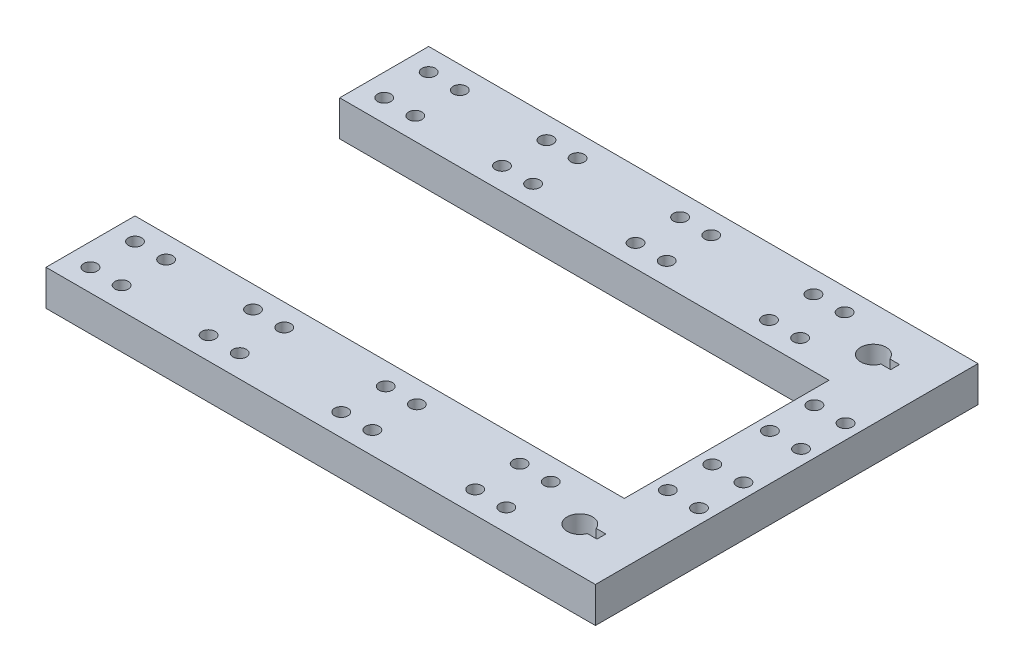
SolidWorks part; units mm, degrees
ref_plane "Front Plane" through (0, 0, 0) normal (0, 0, 1) x (1, 0, 0)
ref_plane "Top Plane" through (0, 0, 0) normal (0, 1, 0) x (1, 0, 0)
ref_plane "Right Plane" through (0, 0, 0) normal (1, 0, 0) x (0, 0, -1)
sketch "Sketch1" plane through (0, 0, 0) normal (0, 1, 0) x (1, 0, 0)
  line L0 (130.9822, 32.9968) -> (21, 32.9968)
  line L6 (130.9822, 32.9968) -> (130.9822, 40.4968)
  line L7 (21, 32.9968) -> (21, 42.9968)
  line L8 (21, 42.9968) -> (144.4822, 42.9968)
  line L9 (130.9822, 32.9968) -> (130.9822, -33.0032)
  line L10 (144.4822, 42.9968) -> (144.4822, 40.4968)
  line L11 (130.9822, -33.0032) -> (20.9822, -33.0032)
  line L12 (21, 32.9968) -> (21, 22.9968)
  line L13 (21, 22.9968) -> (144.4822, 22.9968)
  line L14 (20.9822, -33.0032) -> (20.9822, -23.0032)
  line L15 (20.9822, -23.0032) -> (144.4822, -23.0032)
  line L16 (130.9822, 32.9968) -> (144.4822, 32.9968)
  line L17 (144.4822, 32.9968) -> (144.4822, 40.4968)
  line L18 (144.4822, 40.4968) -> (130.9822, 40.4968)
  line L19 (144.4822, 32.9968) -> (144.4822, -40.5032)
  line L20 (144.4822, -40.5032) -> (130.9822, -40.5032)
  line L21 (20.9822, -33.0032) -> (20.9822, -43.0032)
  line L22 (20.9822, -43.0032) -> (144.4822, -43.0032)
  line L23 (144.4822, -43.0032) -> (144.4822, -40.5032)
  line L24 (26, 32.9968) -> (56, 32.9968)
  line L25 (133.85, 33.9968) -> (133.67, 33.9968)
  line L26 (26, 32.9968) -> (56, 32.9968)
  line L27 (133.85, 31.9968) -> (133.67, 31.9968)
  line L28 (130.9822, -33.0032) -> (133.8322, -33.0032)
  line L29 (56, 32.9968) -> (86, 32.9968)
  line L30 (86, 32.9968) -> (116, 32.9968)
  line L31 (133.8322, -32) -> (132.7951, -32)
  line L32 (133.8322, -34) -> (132.5224, -34)
  line L33 (21, 32.9968) -> (26, 32.9968)
  line L34 (26, 32.9968) -> (26, 27.9968)
  line L35 (26, 27.9968) -> (26, 37.9968)
  line L36 (26, 27.9968) -> (33, 27.9968)
  line L37 (20.9822, -33.0032) -> (25.9822, -33.0032)
  line L38 (25.9822, -33.0032) -> (25.9822, -28.0032)
  line L39 (25.9822, -28.0032) -> (25.9822, -38.0032)
  line L40 (25.9822, -38.0032) -> (32.9822, -38.0032)
  line L41 (133.85, 33.9968) -> (135.85, 33.9968)
  line L42 (135.85, 33.9968) -> (135.85, 31.9968)
  line L43 (135.85, 31.9968) -> (133.85, 31.9968)
  line L44 (133.8322, -32) -> (135.8322, -32)
  line L45 (135.8322, -32) -> (135.8322, -34)
  line L46 (135.8322, -34) -> (133.8322, -34)
  line L47 (25.9822, -33.0032) -> (55.9822, -33.0032)
  line L48 (55.9822, -33.0032) -> (85.9822, -33.0032)
  line L49 (85.9822, -33.0032) -> (115.9822, -33.0032)
  line L50 (144.4822, 22.9968) -> (137.7322, 22.9968)
  line L51 (137.7322, 22.9968) -> (137.7322, 11.4968)
  line L52 (137.7322, -23.0032) -> (137.7322, -11.5032)
  line L53 (132.5224, -34) -> (132.5224, -32)
  line L54 (132.5224, -32) -> (132.7951, -32)
  circle A6 centre (130.9822, 32.9968) radius 2.8678
  circle A7 centre (130.9822, -33.0032) radius 2.85
  circle A8 centre (26, 37.9968) radius 1.5
  circle A9 centre (26, 27.9968) radius 1.5
  circle A10 centre (33, 27.9968) radius 1.5
  circle A11 centre (33, 37.9968) radius 1.5
  circle A12 centre (25.9822, -28.0032) radius 1.5
  circle A13 centre (25.9822, -38.0032) radius 1.5
  circle A14 centre (32.9822, -38.0032) radius 1.5
  circle A15 centre (32.9822, -28.0032) radius 1.5
  circle A16 centre (52.4866, 37.9897) radius 1.5
  circle A17 centre (52.4866, 27.9897) radius 1.5
  circle A18 centre (59.4866, 27.9897) radius 1.5
  circle A19 centre (59.4866, 37.9897) radius 1.5
  circle A20 centre (82.502, 37.9995) radius 1.5
  circle A21 centre (82.502, 27.9995) radius 1.5
  circle A22 centre (89.502, 27.9995) radius 1.5
  circle A23 centre (89.502, 37.9995) radius 1.5
  circle A24 centre (112.5021, 37.9916) radius 1.5
  circle A25 centre (112.5021, 27.9916) radius 1.5
  circle A26 centre (119.5021, 27.9916) radius 1.5
  circle A27 centre (119.5021, 37.9916) radius 1.5
  circle A28 centre (52.4752, -27.9515) radius 1.5
  circle A29 centre (52.4752, -37.9515) radius 1.5
  circle A30 centre (59.4752, -37.9515) radius 1.5
  circle A31 centre (59.4752, -27.9515) radius 1.5
  circle A32 centre (82.3435, -28.0027) radius 1.5
  circle A33 centre (82.3435, -38.0027) radius 1.5
  circle A34 centre (89.3435, -38.0027) radius 1.5
  circle A35 centre (89.3435, -28.0027) radius 1.5
  circle A36 centre (112.4648, -28.0139) radius 1.5
  circle A37 centre (112.4648, -38.0139) radius 1.5
  circle A38 centre (119.4648, -38.0139) radius 1.5
  circle A39 centre (119.4648, -28.0139) radius 1.5
  circle A40 centre (134.1997, 16.4984) radius 1.5
  circle A41 centre (134.1997, 6.4984) radius 1.5
  circle A42 centre (141.1997, 6.4984) radius 1.5
  circle A43 centre (141.1997, 16.4984) radius 1.5
  circle A44 centre (134.2466, -6.4937) radius 1.5
  circle A45 centre (134.2466, -16.4937) radius 1.5
  circle A46 centre (141.2466, -16.4937) radius 1.5
  circle A47 centre (141.2466, -6.4937) radius 1.5
extrude "Boss-Extrude3" add sketch "Sketch1" along normal blind 8
